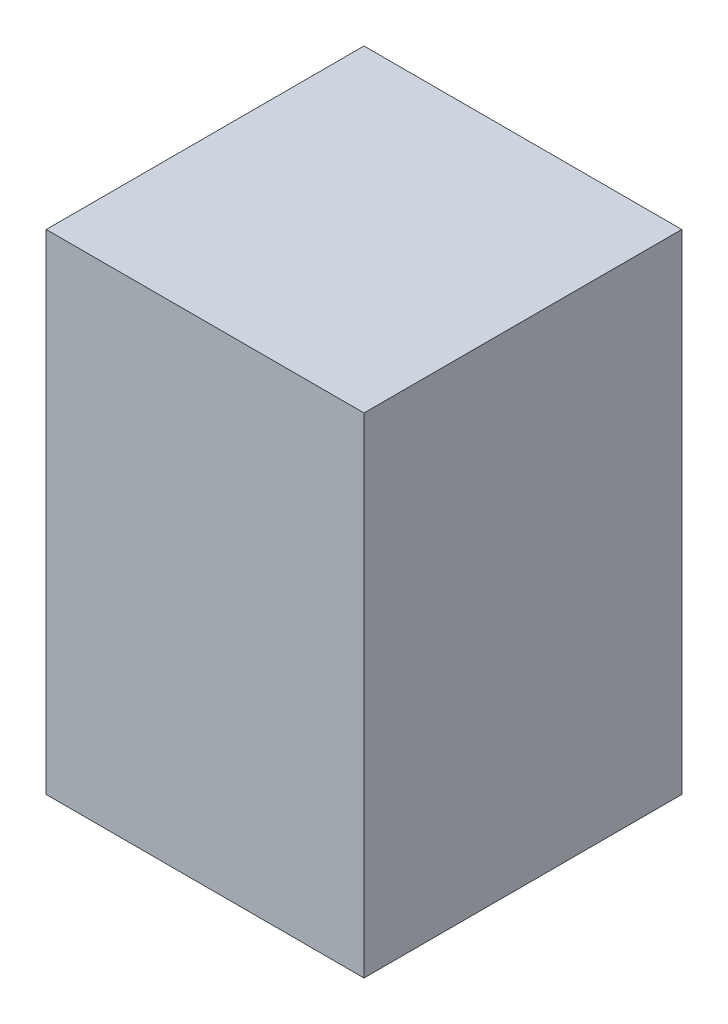
SolidWorks part; units mm, degrees
ref_plane "Alzado" through (0, 0, 0) normal (0, 0, 1) x (1, 0, 0)
ref_plane "Planta" through (0, 0, 0) normal (0, 1, 0) x (1, 0, 0)
ref_plane "Vista lateral" through (0, 0, 0) normal (1, 0, 0) x (0, 0, -1)
sketch "Croquis1" plane through (0, 0, 0) normal (0, 1, 0) x (1, 0, 0)
  line L1 (-250, -250) -> (250, -250)
  line L2 (-250, -250) -> (-250, 250)
  line L3 (-250, 250) -> (250, 250)
  line L4 (250, -250) -> (250, 250)
  line L5 (-250, -250) -> (250, 250) construction
  line L6 (-250, 250) -> (250, -250) construction
  point P0 (0, 0)
  dimension "D1" = 500
  dimension "D2" = 500
extrude "Saliente-Extruir1" add sketch "Croquis1" along normal blind 770
